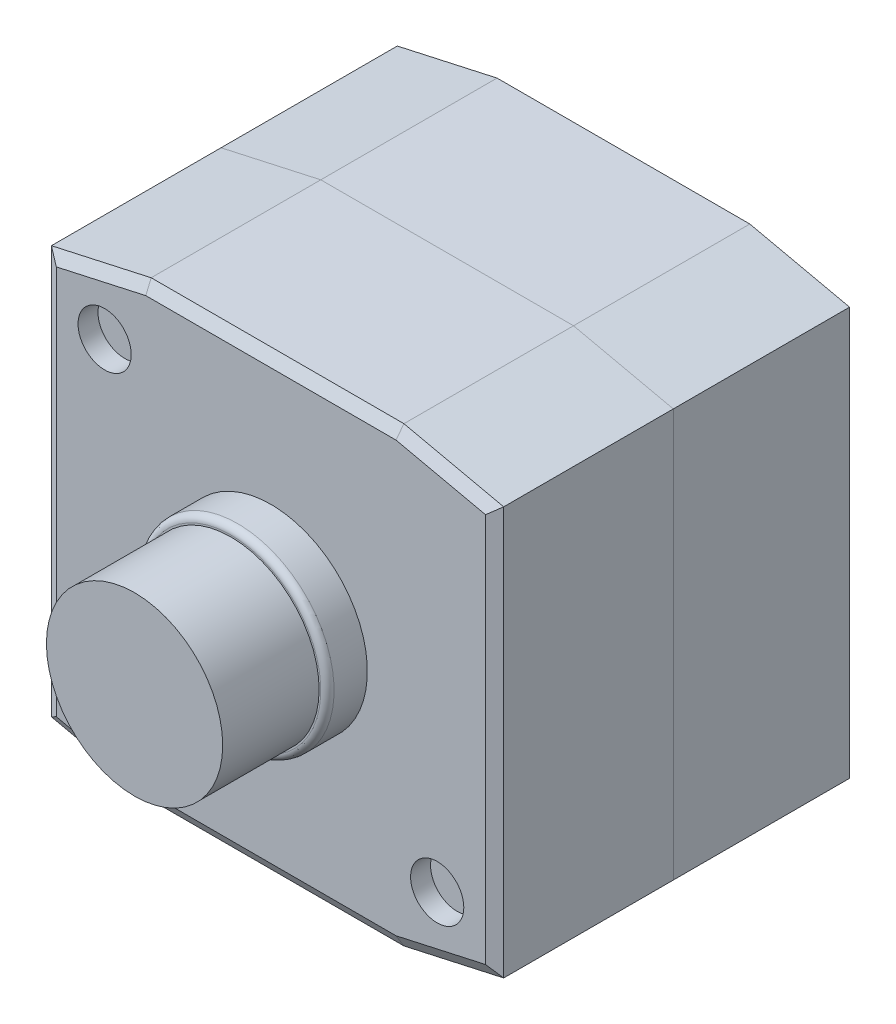
SolidWorks part; units mm, degrees
material "FASTENER MATERIAL PLATED"
ref_plane "Front Plane" through (0, 0, 0) normal (0, 0, 1) x (1, 0, 0)
ref_plane "Top Plane" through (0, 0, 0) normal (0, 1, 0) x (1, 0, 0)
ref_plane "Right Plane" through (0, 0, 0) normal (1, 0, 0) x (0, 0, -1)
ref_plane "Plane1" through (0, 34, 0) normal (0, -1, 0) x (1, 0, 0)
ref_plane "Plane2" through (0, 0, 59) normal (0, 0, 1) x (1, 0, 0)
sketch "Sketch4" plane through (0, 0, 59) normal (0, 0, 1) x (1, 0, 0)
  circle A0 centre (0, 34) radius 14.5
extrude "Boss-Extrude3" add sketch "Sketch4" against normal blind 6
ref_plane "Plane3" through (0, 0, 53) normal (0, 0, 1) x (1, 0, 0)
sketch "Sketch5" plane through (0, 0, 53) normal (0, 0, 1) x (1, 0, 0)
  line L0 (-19, 0) -> (19, 0)
  line L1 (19, 0) -> (34, 3.3254)
  line L2 (34, 3.3254) -> (34, 64.6746)
  line L3 (34, 64.6746) -> (19, 68)
  line L4 (19, 68) -> (-19, 68)
  line L5 (-19, 68) -> (-34, 64.6746)
  line L6 (-34, 64.6746) -> (-34, 3.3254)
  line L7 (-34, 3.3254) -> (-19, 0)
extrude "Boss-Extrude4" add sketch "Sketch5" against normal blind 26.5
hole_wizard "Ø8.0 (8) Diameter Hole1" positions "Sketch9" profile "Sketch8" hole size "Ø8.0" standard "ANSI Metric"
sketch "Sketch9" plane through (0, 0, 53) normal (0, 0, 1) x (1, 0, 0)
  point P0 (-25, 57.5)
  point P1 (25, 10.5)
sketch "Sketch8" plane through (-25, 57.5, 53) normal (1, 0, 0) x (0, -1, 0)
  line L0 (0, 0) -> (0, 3)
  line L1 (0, 3) -> (4, 3)
  line L2 (4, 3) -> (4, 0)
  line L5 (4, 0) -> (0, 0)
  line L10 (0, 3) -> (-4, 3) construction
  line L11 (0, -6.35) -> (0, 107.95) construction
  dimension "Hole Dia." = 8
  dimension "Hole Depth" = 3
  dimension "Drill Angle" = 180
chamfer "Chamfer1" distance 1.7321 angle 30 7 edges at (26.5, 66.3373, 53) (0, 68, 53) (-26.5, 66.3373, 53) (-34, 34, 53) (-26.5, 1.6627, 53) (0, 0, 53) (26.5, 1.6627, 53)
chamfer "Chamfer2" distance 1 angle 60 1 edges at (34, 34, 53)
fillet "Fillet2" [suppressed] radius 4.5
fillet "Fillet3" radius 1 1 edges at (-14.5, 34, 59)
ref_plane "Plane5" through (0, 0, 53) normal (0, 0, -1) x (-1, 0, 0)
sketch "Sketch38" plane through (0, 0, 53) normal (0, 0, -1) x (-1, 0, 0)
  line L8 (19, 0) -> (34, 3.3254)
  line L9 (34, 3.3254) -> (34, 64.6746)
  line L10 (34, 64.6746) -> (19, 68)
  line L11 (19, 68) -> (-19, 68)
  line L12 (-19, 68) -> (-34, 64.6746)
  line L13 (-34, 64.6746) -> (-34, 3.3254)
  line L14 (-34, 3.3254) -> (-19, 0)
  line L15 (-19, 0) -> (19, 0)
ref_plane "Plane6" through (0, 0, 26.5) normal (0, 0, -1) x (-1, 0, 0)
sketch "Sketch40" plane through (0, 0, 26.5) normal (0, 0, -1) x (-1, 0, 0)
  line L0 (34, 3.3254) -> (34, 64.6746)
  line L1 (34, 64.6746) -> (19, 68)
  line L2 (19, 68) -> (-19, 68)
  line L3 (-19, 68) -> (-34, 64.6746)
  line L4 (-34, 64.6746) -> (-34, 3.3254)
  line L5 (-34, 3.3254) -> (-19, 0)
  line L6 (-19, 0) -> (19, 0)
  line L7 (19, 0) -> (34, 3.3254)
extrude "Boss-Extrude7" add sketch "Sketch40" along normal blind 26.5 separate body
sketch "Sketch41" plane through (0, 0, 59) normal (0, 0, 1) x (1, 0, 0)
  circle A0 centre (0, 34) radius 13.25
extrude "Boss-Extrude8" add sketch "Sketch41" along normal blind 14.5
